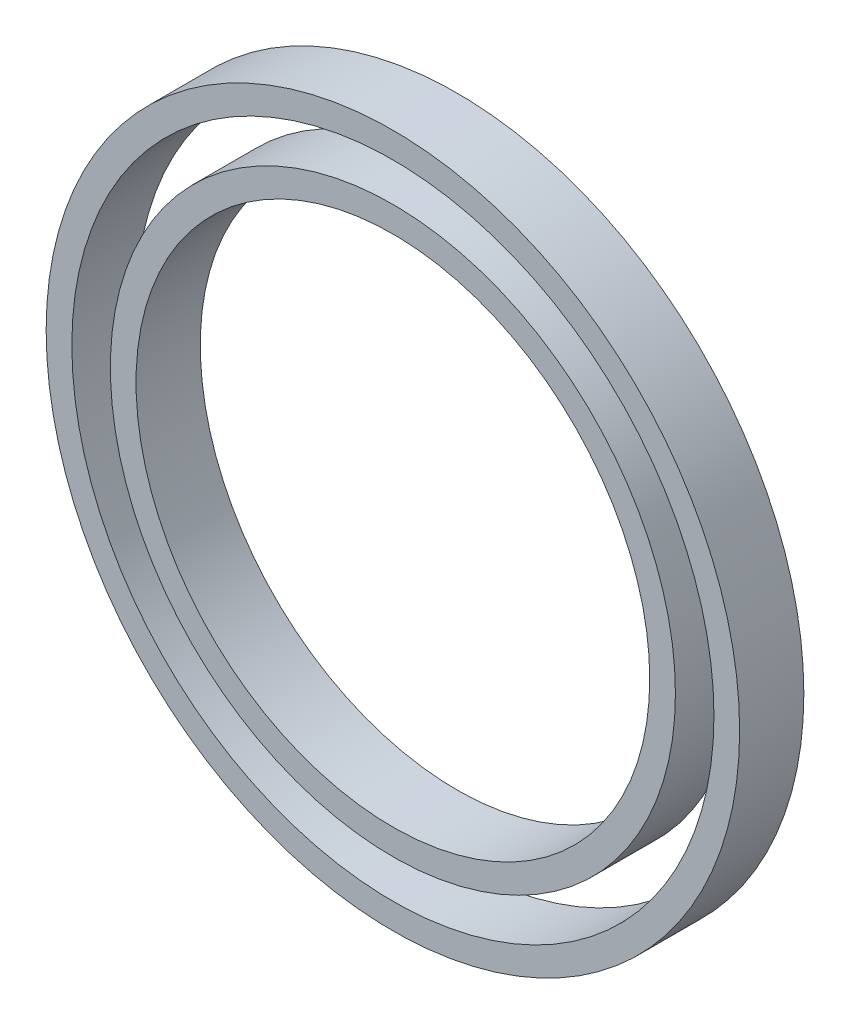
SolidWorks part; units mm, degrees
ref_plane "Front Plane" through (0, 0, 0) normal (0, 0, 1) x (1, 0, 0)
ref_plane "Top Plane" through (0, 0, 0) normal (0, 1, 0) x (1, 0, 0)
ref_plane "Right Plane" through (0, 0, 0) normal (1, 0, 0) x (0, 0, -1)
sketch "Sketch1" plane through (0, 0, 0) normal (0, 0, 1) x (1, 0, 0)
  circle A0 centre (0, 0) radius 20
  circle A1 centre (0, 0) radius 22
  circle A2 centre (0, 0) radius 25
  circle A3 centre (0, 0) radius 27
extrude "Boss-Extrude3" add sketch "Sketch1" along normal blind 5 contours A3 | A2 | A1 | A0
